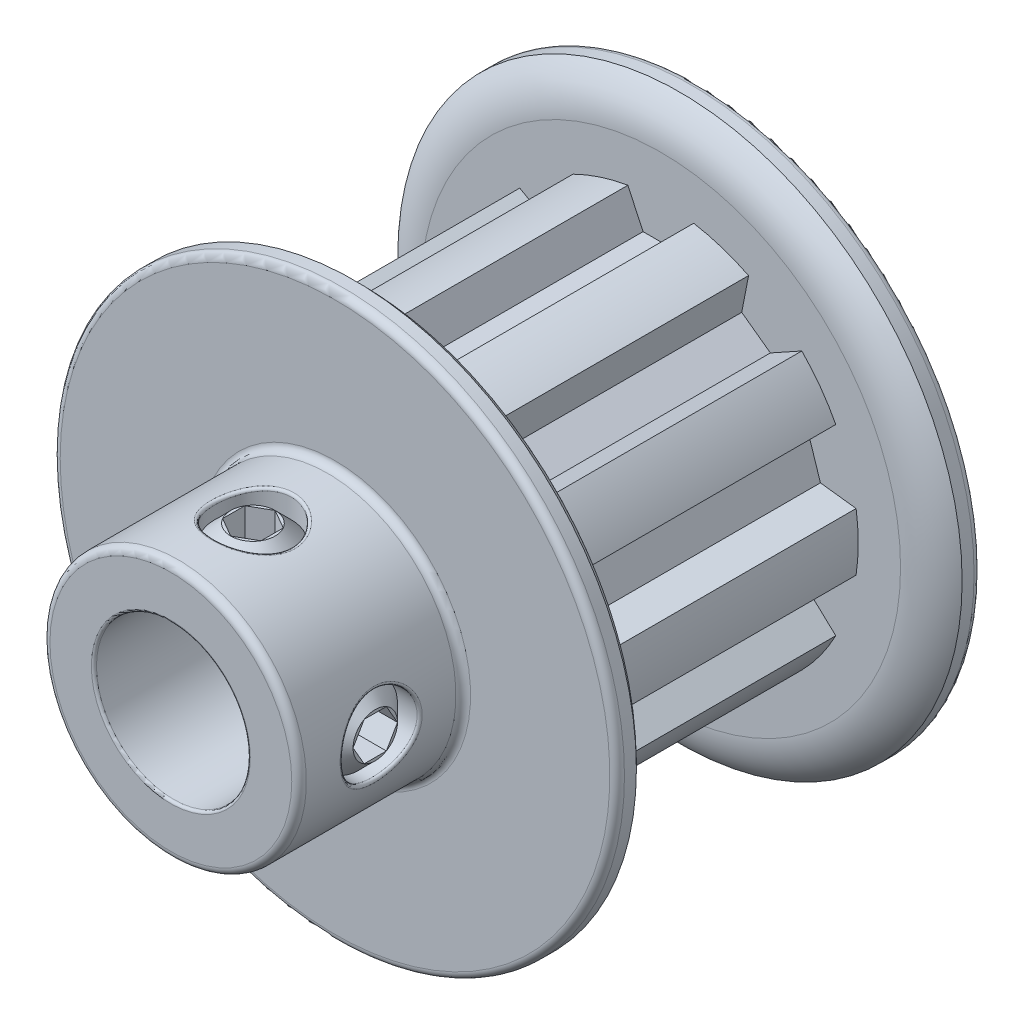
SolidWorks part; units mm, degrees
ref_plane "Front Plane" through (0, 0, 0) normal (0, 0, 1) x (1, 0, 0)
ref_plane "Top Plane" through (0, 0, 0) normal (0, 1, 0) x (1, 0, 0)
ref_plane "Right Plane" through (0, 0, 0) normal (1, 0, 0) x (0, 0, -1)
sketch "Sketch1" plane through (0, 0, 0) normal (0, 0, 1) x (1, 0, 0)
  line L0 (-1.2827, 7.5903) -> (-0.6905, 6.3202)
  line L1 (-0.6905, 6.3202) -> (0.6905, 6.3202)
  line L2 (0.6905, 6.3202) -> (1.2827, 7.5903)
  line L3 (-1.2827, 7.5903) -> (1.2827, 7.5903)
  line L4 (0, 0) -> (0, 6.3202) construction
  line L5 (0, 6.3202) -> (0, 8.6062) construction
  circle A0 centre (0, 0) radius 8.1 construction
  circle A1 centre (0, 0) radius 11 construction
  circle A2 centre (0, 0) radius 7.6979 construction
  point P6 (0, 7.5903)
  point P11 (0, 8.1)
  point P13 (0, 11)
  point P14 (0, 7.6979)
  dimension "Pitch Diameter" = 16.2
  dimension "OD" = 22
  dimension "D5" = 50
  dimension "D6" = 2.5654
  dimension "D4" = 1.27
  dimension "D3" = 2.286
  dimension "D2" = 0.5062
sketch "Sketch2" plane through (0, 0, 0) normal (1, 0, 0) x (0, 0, -1)
  line L0 (-10.3, 3) -> (10.3, 3) construction
  line L1 (-10.3, 3) -> (-10.3, 5) construction
  line L2 (-10.3, 5) -> (-3.9, 5) construction
  line L3 (-3.9, 5) -> (-3.9, 11) construction
  line L4 (-3.9, 11) -> (-2.4, 11) construction
  line L5 (-2.4, 11) -> (-2.4, 7.6979) construction
  line L6 (-2.4, 7.6979) -> (8.8, 7.6979) construction
  line L7 (8.8, 7.6979) -> (8.8, 11) construction
  line L8 (8.8, 11) -> (10.3, 11) construction
  line L9 (10.3, 11) -> (10.3, 3) construction
  line L10 (-10.3, 0) -> (10.3, 0) construction
  line L13 (-3.9, 11) -> (-3.15, 11) construction
  line L14 (-2.4, 9.3489) -> (-2.4, 7.6979) construction
  line L15 (8.8, 7.6979) -> (8.8, 9.3489) construction
  line L16 (9.55, 11) -> (10.3, 11) construction
  arc A0 (-2.4, 9.3489) -> (-3.15, 11) centre (-4.5923, 9.3489) ccw construction
  arc A1 (8.8, 9.3489) -> (9.55, 11) centre (10.9923, 9.3489) cw construction
  point P12 (-2.4, 9.3489)
  point P14 (-3.15, 11)
  point P20 (8.8, 9.3489)
  point P21 (9.55, 11)
  point P25 (8.8, 0)
  point P26 (-2.4, 0)
  dimension "Overall Width" = 20.6
  dimension "Outside Width" = 14.2
  dimension "Inside Width" = 11.2
  dimension "Hub Diameter" = 10
  dimension "For Shaft Diameter" = 6
sketch "Sketch7" plane through (0, 0, 0) normal (1, 0, 0) x (0, 0, -1)
  line L0 (-10.3, 3) -> (-10.3, 5) construction
  line L1 (-10.3, 5) -> (-3.9, 5) construction
  line L2 (-3.9, 5) -> (-3.9, 11) construction
  line L3 (-3.9, 11) -> (-3.15, 11) construction
  line L4 (-2.4, 9.3489) -> (-2.4, 7.6979) construction
  line L5 (-2.4, 7.6979) -> (8.8, 7.6979) construction
  line L6 (8.8, 7.6979) -> (8.8, 9.3489) construction
  line L7 (9.55, 11) -> (10.3, 11) construction
  line L8 (10.3, 11) -> (10.3, 3) construction
  line L9 (-10.3, 3) -> (10.3, 3) construction
  line L10 (-10.3, 3) -> (-10.3, 5)
  line L11 (-10.3, 5) -> (-3.9, 5)
  line L12 (-3.9, 5) -> (-3.9, 11)
  line L13 (-3.9, 11) -> (-3.15, 11)
  line L14 (-2.4, 9.3489) -> (-2.4, 7.6979)
  line L15 (-2.4, 7.6979) -> (8.8, 7.6979)
  line L16 (8.8, 7.6979) -> (8.8, 9.3489)
  line L17 (9.55, 11) -> (10.3, 11)
  line L18 (10.3, 11) -> (10.3, 3)
  line L19 (-10.3, 3) -> (10.3, 3)
  arc A0 (-2.4, 9.3489) -> (-3.15, 11) centre (-4.5923, 9.3489) ccw construction
  arc A1 (9.55, 11) -> (8.8, 9.3489) centre (10.9923, 9.3489) ccw construction
  arc A2 (-2.4, 9.3489) -> (-3.15, 11) centre (-4.5923, 9.3489) ccw
  arc A3 (9.55, 11) -> (8.8, 9.3489) centre (10.9923, 9.3489) ccw
revolve "Revolve1" add sketch "Sketch7" angle 360 about L10
sketch "Sketch3" plane through (0, 0, 0) normal (0, 0, 1) x (1, 0, 0)
  line L0 (-0.6905, 6.3202) -> (0.6905, 6.3202) construction
  line L1 (0.6905, 6.3202) -> (1.2827, 7.5903) construction
  line L2 (-1.2827, 7.5903) -> (-0.6905, 6.3202) construction
  line L3 (-0.6905, 6.3202) -> (0.6905, 6.3202)
  line L4 (0.6905, 6.3202) -> (1.2827, 7.5903)
  line L5 (-1.2827, 7.5903) -> (-0.6905, 6.3202)
  arc A1 (1.2827, 7.5903) -> (-1.2827, 7.5903) centre (0, 0) ccw
  circle A2 centre (0, 0) radius 7.6979 construction
extrude "Cut-Extrude1" cut sketch "Sketch3" against normal up to vertex (8.8 mm away) from vertex at 2.4 starting at point (0, 7.6979, 2.4)
pattern_circular "CirPattern1" count 10 over 360 about axis through (0, 0, 0) along (0, 0, 1) of "Cut-Extrude1"
sketch "Sketch4" plane through (0, 0, 0) normal (0, 1, 0) x (1, 0, 0)
  line L0 (0, -3.9) -> (0, -10.3) construction
  line L3 (0, -10.3) -> (0, 10.3) construction
  line L4 (-5, -3.9) -> (5, -3.9) construction
  line L5 (-5, -10.3) -> (5, -10.3) construction
  circle A0 centre (0, -7.1) radius 1.5
  dimension "D1" = 3
extrude "Cut-Extrude2" cut sketch "Sketch4" along normal through all
ref_plane "Plane1" through (0, 0, 7.1) normal (0, 0, 1) x (1, 0, 0)
sketch "Sketch5" plane through (0, 0, 7.1) normal (0, 0, 1) x (1, 0, 0)
  line L0 (0, 0) -> (0, 5) construction
  line L1 (-1.5, 4.7697) -> (-1.5, 2.5981) construction
  line L2 (-1.5, 4.7697) -> (-1.5, 2.5981) construction
  line L3 (0, 4.7697) -> (0, 3)
  line L4 (0, 3) -> (-0.865, 3)
  line L5 (-1.5, 4.1347) -> (-1.5, 3.635)
  line L6 (-0.865, 4.7697) -> (0, 4.7697)
  line L7 (-1.5, 4.1347) -> (-0.865, 4.7697)
  line L8 (-1.5, 3.635) -> (-0.865, 3)
  line L9 (0, 11) -> (0, 3) construction
  line L10 (0, 3) -> (0, 5) construction
  point P13 (-1.5, 3)
  point P15 (-1.5, 4.7697)
revolve "Revolve2" add sketch "Sketch5" angle 360 mid plane about L0
sketch "Sketch6" plane through (0, 4.7697, 0) normal (0, -1, 0) x (-1, 0, 0)
  line L1 (0, -6.234) -> (-0.75, -6.667)
  line L2 (-0.75, -6.667) -> (-0.75, -7.533)
  line L3 (-0.75, -7.533) -> (0, -7.966)
  line L4 (0, -7.966) -> (0.75, -7.533)
  line L5 (0.75, -7.533) -> (0.75, -6.667)
  line L6 (0.75, -6.667) -> (0, -6.234)
  circle A0 centre (0, -7.1) radius 0.75 construction
  dimension "D1" = 1.5
extrude "Cut-Extrude3" cut sketch "Sketch6" along normal blind 1.125
pattern_circular "CirPattern2" count 2 every 90 about axis through (0, 0, 0) along (0, 0, 1) of "Cut-Extrude2", "Revolve2", "Cut-Extrude3"
fillet "Fillet1" radius 0.2857 4 edges at (11, 0, -10.3) (11, 0, 3.9) (5, 0, 3.9) (5, 0, 10.3)
fillet "Fillet2" radius 0.1 4 edges at (3, 0, 10.3) (4.9926, -0.2714, 8.5752) (0.2714, 4.9926, 8.5752) (3, 0, -10.3)
equation "\"D1@Sketch4\" = \"For Shaft Diameter@Sketch2\"/2"
equation "\"D1@Sketch6\" = \"D1@Sketch4\"/2"
equation "\"D1@Cut-Extrude3\" = \"D1@Sketch6\"*.75"
equation "\"D1@Fillet1\"=\"Hub Diameter@Sketch2\" / 35"
equation "\"D2@Sketch1\"=\"Pitch Diameter@Sketch1\"/32"
equation "\"D1@Fillet2\"=\"Hub Diameter@Sketch2\"*.01"
